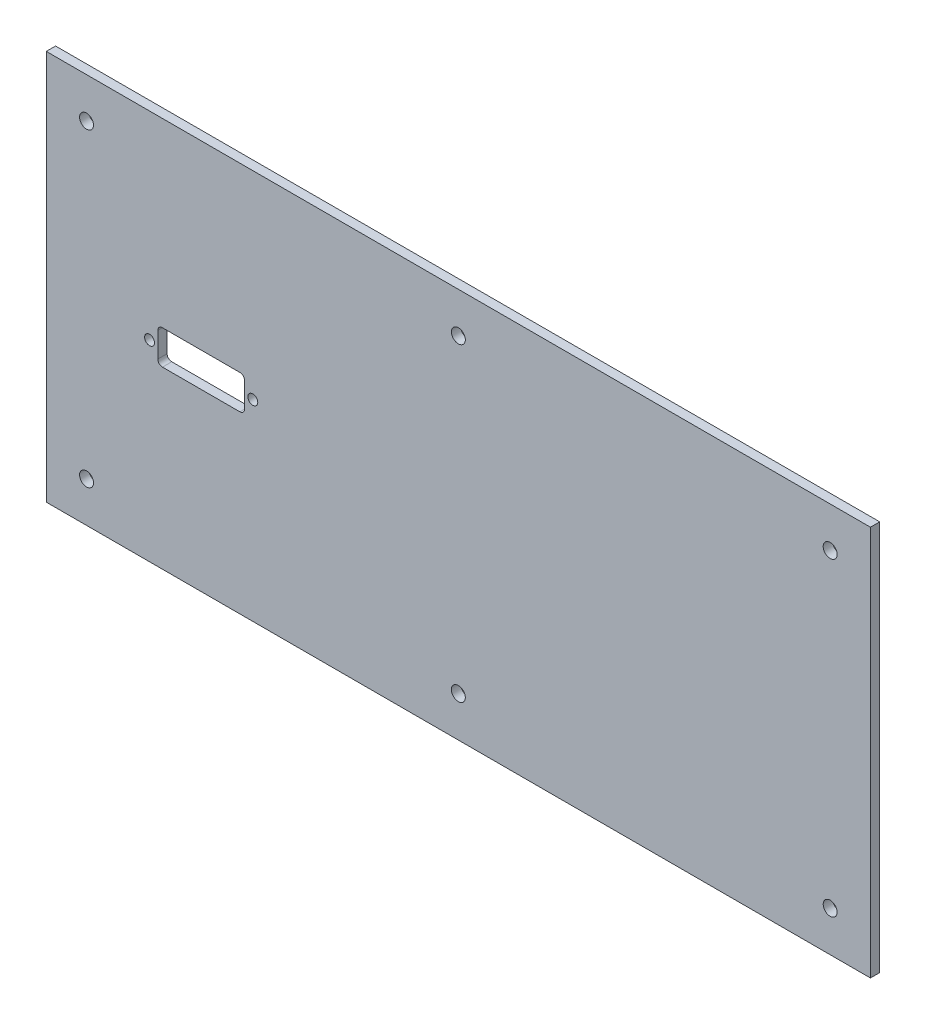
SolidWorks part; units mm, degrees
ref_plane "Спереди" through (0, 0, 0) normal (0, 0, 1) x (1, 0, 0)
ref_plane "Сверху" through (0, 0, 0) normal (0, 1, 0) x (1, 0, 0)
ref_plane "Справа" through (0, 0, 0) normal (1, 0, 0) x (0, 0, -1)
sketch "Эскиз1" plane through (0, 0, 236) normal (0, 0, 1) x (1, 0, 0)
  line L4 (23, -3) -> (23, 123)
  line L5 (-243, -3) -> (23, -3)
  line L6 (-243, 123) -> (-243, -3)
  line L7 (23, 123) -> (-243, 123)
  line L8 (23, -3) -> (23, 123)
  line L9 (-243, -3) -> (23, -3)
  line L10 (-243, 123) -> (-243, -3)
  line L11 (23, 123) -> (-243, 123)
  dimension "D1" = 0
extrude "Бобышка-Вытянуть1" add sketch "Эскиз1" along normal blind 3
sketch "Эскиз2" plane through (0, 0, 239) normal (0, 0, 1) x (1, 0, 0)
  line L0 (-230, 110) -> (10, 110) construction
  line L1 (-230, 110) -> (-230, 10) construction
  line L2 (10, 110) -> (10, 10) construction
  line L3 (-230, 10) -> (10, 10) construction
  line L4 (-243, 123) -> (-243, -3) construction
  line L5 (23, 123) -> (-243, 123) construction
  line L6 (23, -3) -> (23, 123) construction
  line L7 (-243, -3) -> (23, -3) construction
  circle A0 centre (-230, 110) radius 2.25
  circle A1 centre (-110, 110) radius 2.25
  circle A2 centre (10, 110) radius 2.25
  circle A3 centre (10, 10) radius 2.25
  circle A4 centre (-110, 10) radius 2.25
  circle A5 centre (-230, 10) radius 2.25
  dimension "D5" = 4.5
  dimension "D6" = 4.5
  dimension "D7" = 4.5
  dimension "D8" = 4.5
  dimension "D9" = 4.5
  dimension "D10" = 4.5
  dimension "D1" = 13
  dimension "D2" = 13
  dimension "D3" = 13
  dimension "D4" = 13
extrude "Вырез-Вытянуть1" cut sketch "Эскиз2" against normal through all
sketch "Sketch1" plane through (0, 0, 239) normal (0, 0, 1) x (1, 0, 0)
  line L0 (-243, 59) -> (-179, 59) construction
  line L1 (-243, 123) -> (-243, -3) construction
  line L2 (23, 123) -> (-243, 123) construction
  line L3 (-207, 63) -> (-207, 55)
  line L4 (-205.5, 64.5) -> (-180.5, 64.5)
  line L5 (-205.5, 53.5) -> (-180.5, 53.5)
  line L6 (-179, 63) -> (-179, 55)
  line L7 (-207, 59) -> (-179, 59) construction
  line L8 (-193, 64.5) -> (-193, 53.5) construction
  line L10 (-209.66, 59) -> (-176.34, 59) construction
  circle A0 centre (-209.66, 59) radius 1.6
  circle A1 centre (-176.34, 59) radius 1.6
  arc A2 (-180.5, 53.5) -> (-179, 55) centre (-180.5, 55) ccw
  arc A3 (-179, 63) -> (-180.5, 64.5) centre (-180.5, 63) ccw
  arc A4 (-205.5, 53.5) -> (-207, 55) centre (-205.5, 55) cw
  arc A5 (-205.5, 64.5) -> (-207, 63) centre (-205.5, 63) ccw
  point P17 (-193, 59)
  dimension "D5" = 3.2
  dimension "D6" = 3.2
  dimension "D7" = 33.32
  dimension "D8" = 1.5
  dimension "D1" = 64
  dimension "D2" = 28
  dimension "D3" = 11
  dimension "D4" = 50
extrude "Cut-Extrude1" cut sketch "Sketch1" against normal through all
